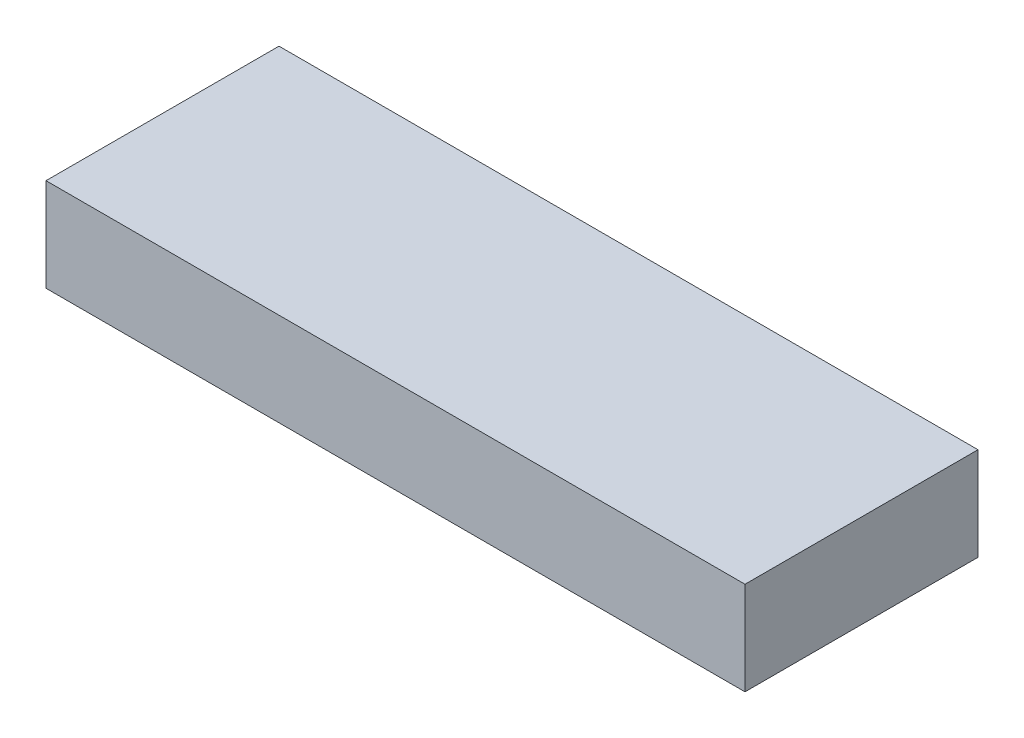
SolidWorks part; units mm, degrees
material " "
ref_plane "Ebene vorne" through (0, 0, 0) normal (0, 0, 1) x (1, 0, 0)
ref_plane "Ebene oben" through (0, 0, 0) normal (0, 1, 0) x (1, 0, 0)
ref_plane "Ebene rechts" through (0, 0, 0) normal (1, 0, 0) x (0, 0, -1)
sketch "Skizze8" plane through (0, 0, 0) normal (0, 1, 0) x (1, 0, 0)
  line L0 (150, 50) -> (-150, -50) construction
  line L1 (-150, 50) -> (150, 50)
  line L2 (-150, 50) -> (-150, -50)
  line L3 (-150, -50) -> (150, -50)
  line L4 (150, 50) -> (150, -50)
  dimension "D1" = 300
  dimension "D2" = 100
extrude "Aufsatz-Linear austragen1" add sketch "Skizze8" along normal mid plane 40 separate body
